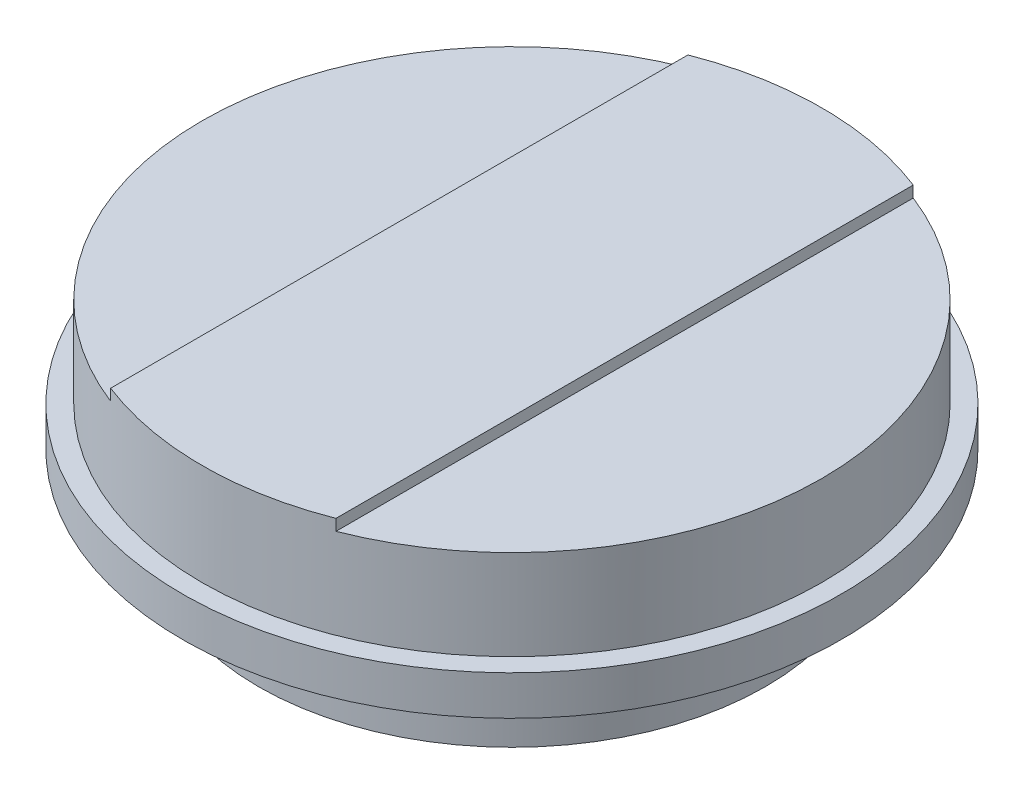
SolidWorks part; units mm, degrees
ref_plane "前基準面" through (0, 0, 0) normal (0, 0, 1) x (1, 0, 0)
ref_plane "上基準面" through (0, 0, 0) normal (0, 1, 0) x (1, 0, 0)
ref_plane "右基準面" through (0, 0, 0) normal (1, 0, 0) x (0, 0, -1)
sketch "草圖1" plane through (0, 0, 0) normal (0, 0, 1) x (1, 0, 0)
  line L0 (0, 84.4405) -> (0, 0) construction
  line L3 (0, 0) -> (55, 0)
  line L4 (55, 0) -> (55, -16)
  line L5 (55, -16) -> (58.5, -16)
  line L6 (58.5, -16) -> (58.5, -23)
  line L7 (58.5, -23) -> (45, -23)
  line L8 (45, -23) -> (45, -37)
  line L9 (45, -37) -> (10, -37)
  line L10 (10, -37) -> (10, -57)
  line L11 (10, -57) -> (5, -57)
  line L12 (5, -57) -> (5, -39)
  line L13 (5, -39) -> (0, -39)
  line L14 (0, 0) -> (0, -39)
  line L15 (0, 0) -> (0, -84.4405) construction
  point P4 (0, 0)
  point P5 (0, 0)
  dimension "D2" = 110
  dimension "D3" = 117
  dimension "D4" = 90
  dimension "D5" = 20
  dimension "D6" = 10
  dimension "D8" = 16
  dimension "D9" = 7
  dimension "D10" = 14
  dimension "D11" = 18
  dimension "D12" = 20
revolve "旋轉1" add sketch "草圖1" angle 360 about L0
sketch "草圖3" plane through (0, 0, 0) normal (0, 1, 0) x (1, 0, 0)
  line L0 (0, 0) -> (0, 19.0898) construction
  line L1 (-20, 51.2348) -> (-20, -51.2348)
  line L2 (-16.7285, 0) -> (20.3286, 0) construction
  line L3 (20, 51.2348) -> (20, -51.2348)
  arc A0 (-20, 51.2348) -> (20, 51.2348) centre (0, 0) cw
  circle A1 centre (0, 0) radius 55 construction
  circle A2 centre (0, 0) radius 55 construction
  arc A3 (-20, -51.2348) -> (20, -51.2348) centre (0, 0) ccw
  dimension "D1" = 40
extrude "填料-伸長1" add sketch "草圖3" along normal blind 2
